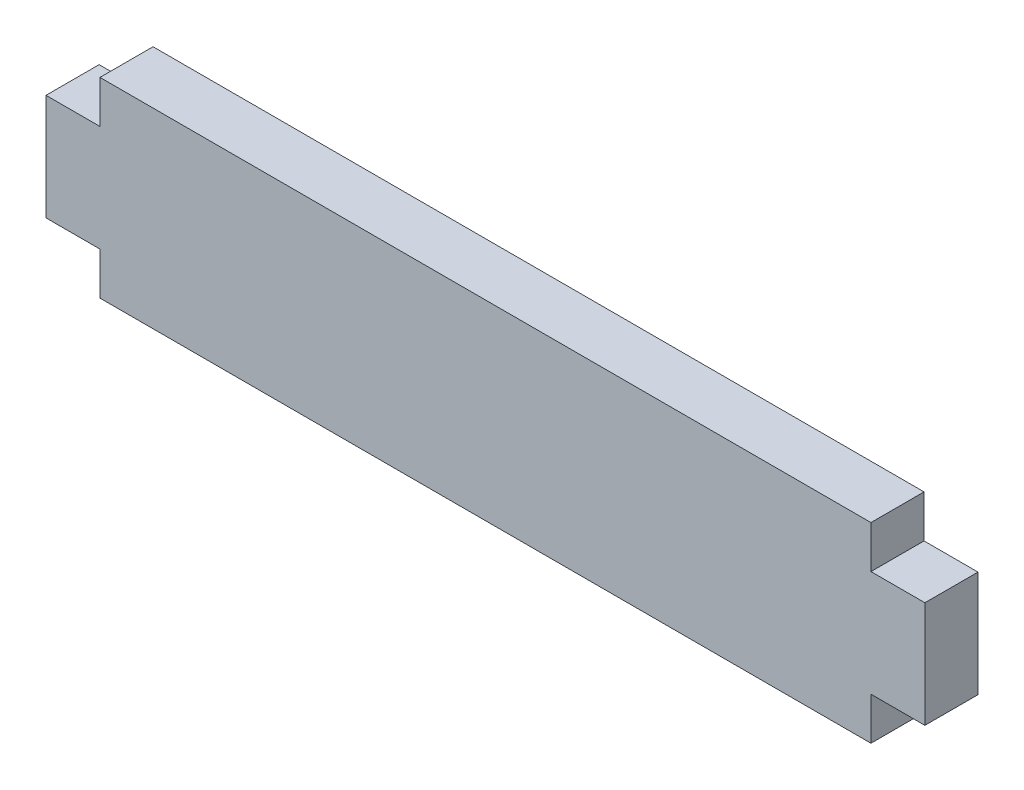
SolidWorks part; units mm, degrees
ref_plane "Front Plane" through (0, 0, 0) normal (0, 0, 1) x (1, 0, 0)
ref_plane "Top Plane" through (0, 0, 0) normal (0, 1, 0) x (1, 0, 0)
ref_plane "Right Plane" through (0, 0, 0) normal (1, 0, 0) x (0, 0, -1)
sketch "Sketch1" plane through (0, 0, 0) normal (0, 0, 1) x (1, 0, 0)
  line L0 (-23.0505, 3.175) -> (-26.2763, 3.175)
  line L1 (-23.0505, -5.715) -> (23.0505, -5.715)
  line L2 (-23.0505, -5.715) -> (-23.0505, -3.175)
  line L3 (-23.0505, 5.715) -> (23.0505, 5.715)
  line L4 (23.0505, -5.715) -> (23.0505, -3.175)
  line L5 (-23.0505, -5.715) -> (23.0505, 5.715) construction
  line L6 (-23.0505, 5.715) -> (23.0505, -5.715) construction
  line L7 (-26.2763, 3.175) -> (-26.2763, -3.175)
  line L8 (-26.2763, -3.175) -> (-23.0505, -3.175)
  line L9 (-23.0505, 3.175) -> (-23.0505, 5.715)
  line L10 (23.0505, 3.175) -> (26.2763, 3.175)
  line L11 (26.2763, 3.175) -> (26.2763, -3.175)
  line L12 (26.2763, -3.175) -> (23.0505, -3.175)
  line L13 (23.0505, 3.175) -> (23.0505, 5.715)
  line L14 (-26.2763, 0) -> (0, 0) construction
  point P0 (0, 0)
  dimension "D1" = 46.101
  dimension "D2" = 11.43
  dimension "D3" = 3.2258
  dimension "D4" = 6.35
  dimension "D7" = 3.2258
  dimension "D8" = 6.35
extrude "Boss-Extrude1" add sketch "Sketch1" along normal blind 3.175
